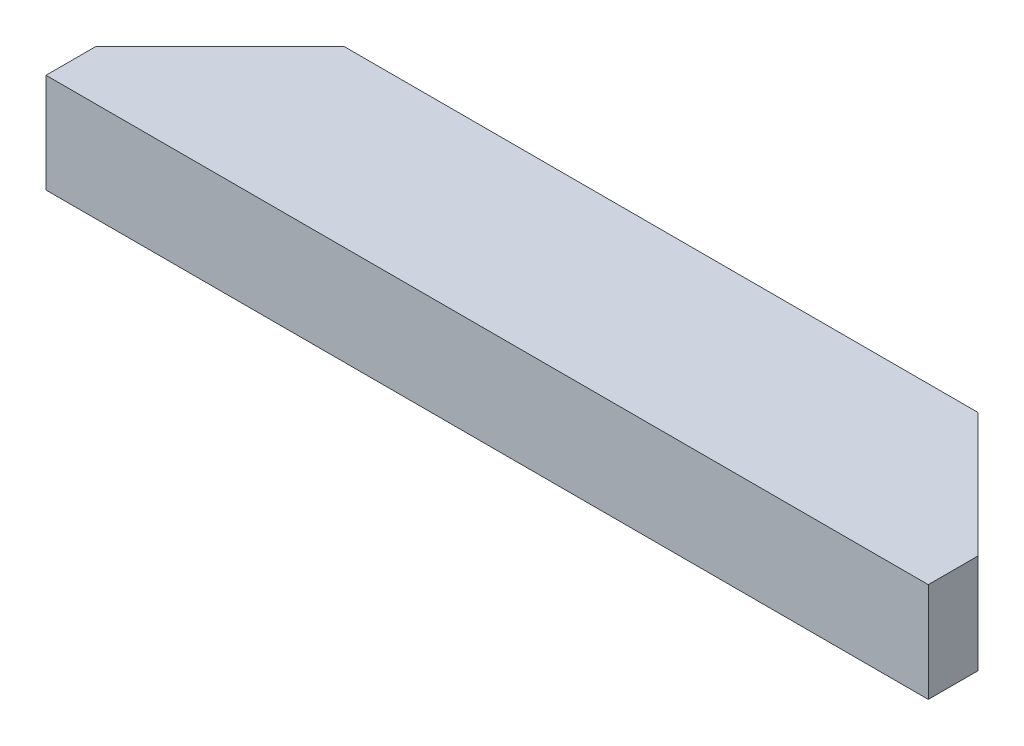
SolidWorks part; units mm, degrees
ref_plane "Front Plane" through (0, 0, 0) normal (0, 0, 1) x (1, 0, 0)
ref_plane "Top Plane" through (0, 0, 0) normal (0, 1, 0) x (1, 0, 0)
ref_plane "Right Plane" through (0, 0, 0) normal (1, 0, 0) x (0, 0, -1)
sketch "Sketch1" plane through (0, 0, 0) normal (0, 1, 0) x (1, 0, 0)
  line L1 (-225.425, -44.45) -> (225.425, -44.45)
  line L2 (-225.425, -44.45) -> (-225.425, 44.45)
  line L3 (-225.425, 44.45) -> (225.425, 44.45)
  line L4 (225.425, -44.45) -> (225.425, 44.45)
  line L5 (-225.425, -44.45) -> (225.425, 44.45) construction
  line L6 (-225.425, 44.45) -> (225.425, -44.45) construction
  point P0 (0, 0)
  dimension "D1" = 450.85
  dimension "D2" = 88.9
extrude "Boss-Extrude1" add sketch "Sketch1" along normal mid plane 50.8
sketch "Sketch2" plane through (0, 25.4, 0) normal (0, 1, 0) x (1, 0, 0)
  line L0 (0, 44.45) -> (0, -44.45) construction
  line L1 (225.425, 44.45) -> (-225.425, 44.45) construction
  line L2 (-225.425, -44.45) -> (225.425, -44.45) construction
  line L5 (225.425, -44.45) -> (225.425, 44.45) construction
  line L10 (225.425, 0) -> (-225.425, 0) construction
  line L11 (-225.425, 44.45) -> (-225.425, -44.45) construction
  line L15 (-225.425, 44.45) -> (-225.425, -19.05)
  line L16 (-225.425, -19.05) -> (-161.925, 44.45)
  line L17 (-161.925, 44.45) -> (-225.425, 44.45)
  line L18 (225.425, -19.05) -> (161.925, 44.45)
  line L19 (225.425, 44.45) -> (225.425, -19.05)
  line L20 (161.925, 44.45) -> (225.425, 44.45)
  dimension "D1" = 63.5
  dimension "D2" = 45
extrude "Cut-Extrude1" cut sketch "Sketch2" against normal through all
